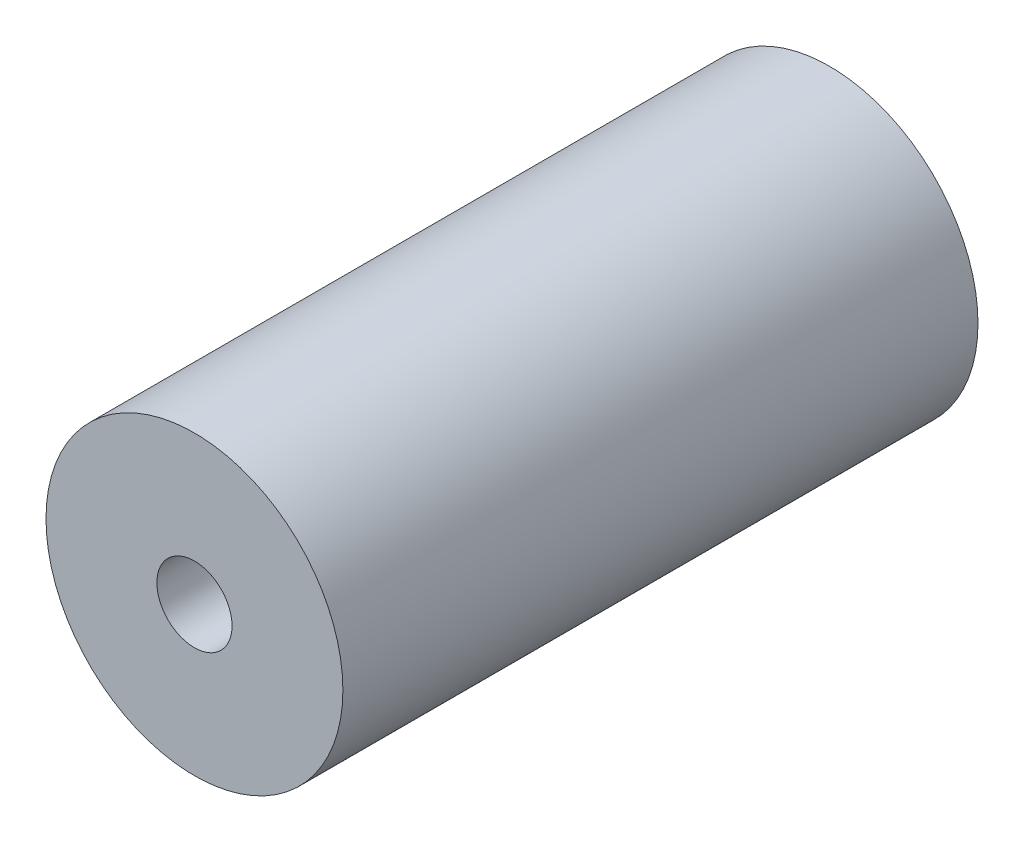
SolidWorks part; units mm, degrees
ref_plane "Front Plane" through (0, 0, 0) normal (0, 0, 1) x (1, 0, 0)
ref_plane "Top Plane" through (0, 0, 0) normal (0, 1, 0) x (1, 0, 0)
ref_plane "Right Plane" through (0, 0, 0) normal (1, 0, 0) x (0, 0, -1)
sketch "Sketch1" plane through (0, 0, 0) normal (0, 0, 1) x (1, 0, 0)
  circle A0 centre (0, 0) radius 1.975
  circle A1 centre (0, 0) radius 0.5
  dimension "D1" = 1
  dimension "D2" = 3.95
extrude "Boss-Extrude1" add sketch "Sketch1" along normal blind 8.45
